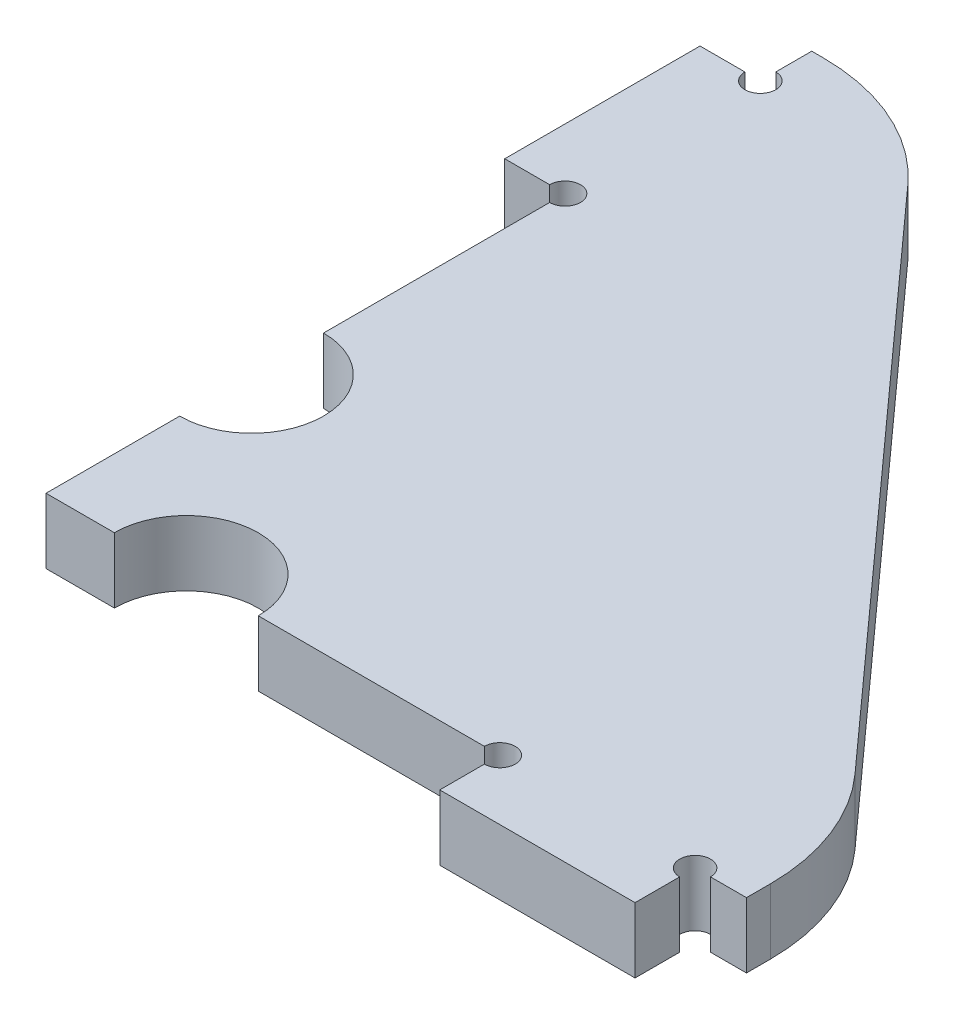
SolidWorks part; units mm, degrees
ref_plane "Front Plane" through (0, 0, 0) normal (0, 0, 1) x (1, 0, 0)
ref_plane "Top Plane" through (0, 0, 0) normal (0, 1, 0) x (1, 0, 0)
ref_plane "Right Plane" through (0, 0, 0) normal (1, 0, 0) x (0, 0, -1)
sketch "Sketch2" plane through (0, 0, 0) normal (0, 1, 0) x (1, 0, 0)
  line L0 (0, 0) -> (44.15, 0)
  line L1 (44.15, 0) -> (44.15, -5.842)
  line L2 (44.15, -5.842) -> (63.15, -5.842)
  line L3 (63.15, -5.842) -> (63.15, 0)
  line L4 (63.15, 0) -> (68.15, 0)
  line L5 (68.15, 0) -> (68.15, 10)
  line L6 (0, 0) -> (0, 50.5)
  line L7 (0, 50.5) -> (-5.87, 50.5)
  line L8 (-5.87, 50.5) -> (-5.87, 69.5)
  line L9 (-5.87, 69.5) -> (0, 69.5)
  line L10 (0, 69.5) -> (0, 74.5)
  line L11 (0, 74.5) -> (10, 74.5)
  line L12 (10, 74.5) -> (68.15, 10)
  dimension "D1" = 44.15
  dimension "D2" = 19
  dimension "D3" = 5.842
  dimension "D4" = 5
  dimension "D5" = 50.5
  dimension "D6" = 19
  dimension "D7" = 5.87
  dimension "D8" = 5
  dimension "D9" = 10
  dimension "D10" = 10
extrude "Boss-Extrude1" add sketch "Sketch2" along normal blind 6.35
sketch "Sketch3" plane through (0, 6.35, 0) normal (0, 1, 0) x (1, 0, 0)
  line L0 (44.15, 0) -> (44.15, -5.842) construction
  line L1 (0, 0) -> (44.15, 0) construction
  line L2 (0, 50.5) -> (0, 0) construction
  circle A0 centre (0, 69.5) radius 1.5
  circle A1 centre (0, 50.5) radius 1.5
  circle A2 centre (44.15, 0) radius 1.5
  circle A3 centre (63.15, 0) radius 1.5
  circle A4 centre (0, 20) radius 7
  circle A5 centre (13.65, 0) radius 7
  dimension "D1" = 20
  dimension "D2" = 13.65
extrude "Cut-Extrude1" cut sketch "Sketch3" against normal through all
fillet "Fillet1" radius 20 2 edges at (68.15, 3.175, -10) (10, 3.175, -74.5)
